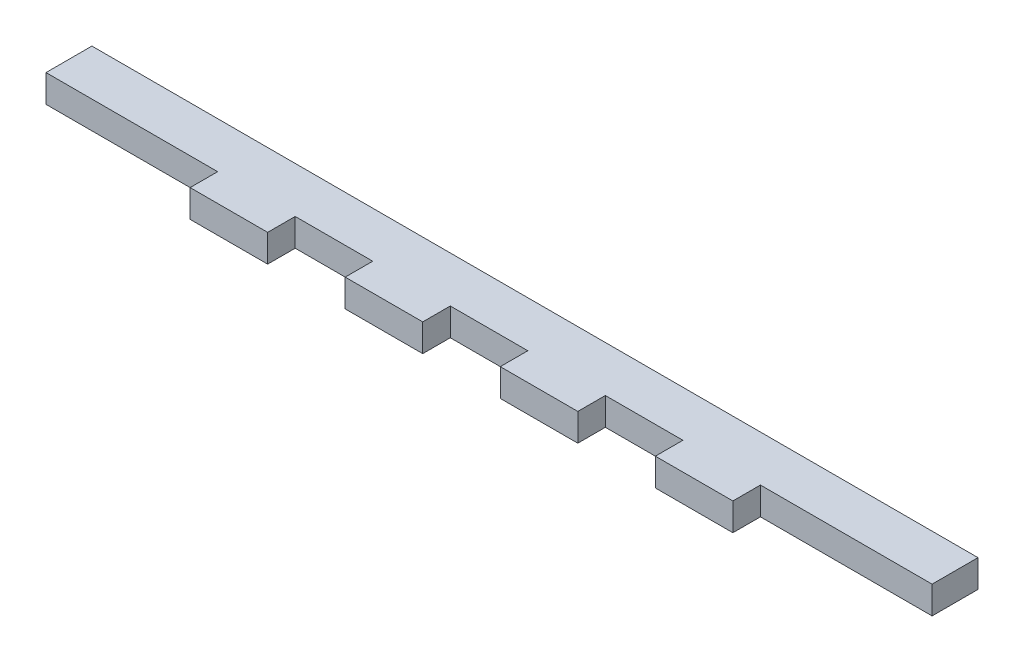
SolidWorks part; units mm, degrees
ref_plane "Front Plane" through (0, 0, 0) normal (0, 0, 1) x (1, 0, 0)
ref_plane "Top Plane" through (0, 0, 0) normal (0, 1, 0) x (1, 0, 0)
ref_plane "Right Plane" through (0, 0, 0) normal (1, 0, 0) x (0, 0, -1)
sketch "Sketch1" plane through (0, 0, 0) normal (0, 1, 0) x (1, 0, 0)
  line L1 (-96.5, 5) -> (96.5, 5)
  line L2 (-96.5, 5) -> (-96.5, -5)
  line L3 (-96.5, -5) -> (96.5, -5)
  line L4 (96.5, 5) -> (96.5, -5)
  line L5 (-96.5, 5) -> (96.5, -5) construction
  line L6 (-96.5, -5) -> (96.5, 5) construction
  point P0 (0, 0)
  dimension "D1" = 193
  dimension "D2" = 10
sketch "Sketch2" plane through (0, 0, 0) normal (0, 0, 1) x (1, 0, 0)
  line L0 (0, 0) -> (0, 6) construction
  line L1 (-96.5, 0) -> (96.5, 0) construction
  dimension "D1" = 6
extrude "Boss-Extrude1" add sketch "Sketch1" along normal up to vertex (6 mm away) contours L2 L3 L4 L1 up to point (0, 6, 0)
sketch "Sketch4" plane through (0, 0, 0) normal (0, -1, 0) x (1, 0, 0)
  line L0 (0, 0) -> (0, 11)
  line L1 (8.4444, 11) -> (-8.4444, 11)
  line L3 (-98.4064, -241.8596) -> (59.5936, -241.8596) construction
  line L4 (-96.5, 5) -> (96.5, 5) construction
  line L5 (-8.4444, 11) -> (-25.3333, 11)
  line L6 (-8.4444, 11) -> (-8.4444, 5)
  line L7 (-8.4444, 5) -> (-25.3333, 5)
  line L8 (-25.3333, 11) -> (-25.3333, 5)
  line L9 (-59.1111, 11) -> (-76, 11)
  line L10 (-25.3333, 5) -> (-42.2222, 5)
  line L11 (-25.3333, 5) -> (-25.3333, 11)
  line L12 (-25.3333, 11) -> (-42.2222, 11)
  line L13 (-42.2222, 5) -> (-42.2222, 11)
  line L14 (-42.2222, 11) -> (-59.1111, 11)
  line L15 (-42.2222, 11) -> (-42.2222, 5)
  line L16 (-42.2222, 5) -> (-59.1111, 5)
  line L17 (-59.1111, 11) -> (-59.1111, 5)
  point P9 (0, 11)
extrude "Boss-Extrude3" add sketch "Sketch4" against normal up to surface (6 mm away) contours L5 L8 L6 M17 | L14 L17 L13 M17 up to face at (0, 6, 0)
mirror "Mirror1" about plane through (0, 0, 0) normal (1, 0, 0) of "Boss-Extrude3"
equation "\"glass_width\"= 181"
equation "\"glass_height\"= 151"
equation "\"glass_thickness\"= 2.5"
equation "\"brood_space\"= 42"
equation "\"t1\"= 6"
equation "\"t2\"= 6"
equation "\"box_depth\"= \"brood_space\" + \"glass_thickness\" + \"glass_thickness\" + \"t2\" + \"t2\""
equation "\"box_width\"= \"glass_width\" + \"t1\" + \"t1\""
equation "\"food_height\"= 70"
equation "\"box_height\"= \"glass_height\" + ( \"t1\" * 3 ) + \"food_height\""
equation "\"D1@Sketch1\"=\"box_width\""
equation "\"D1@Sketch2\"=\"t2\""
equation "\"entry_height\"= 24"
equation "\"entry_diameter\"= 8"
equation "\"food_top_clearance\"= 10"
equation "\"bar_width\"= 20"
equation "\"glassblocker_lower_height\"= 10"
equation "\"lower_edge_stickout\"=6"
